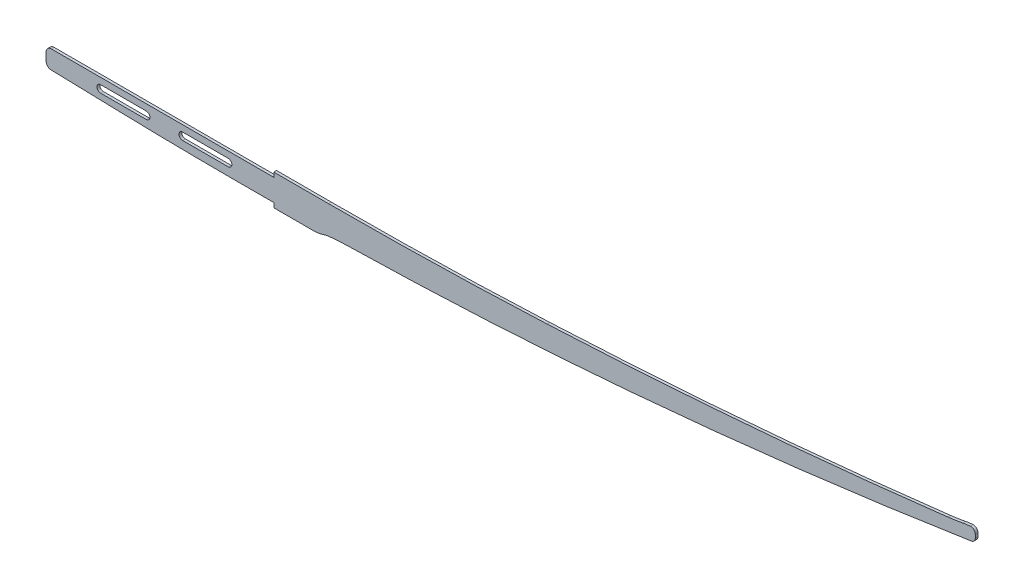
SolidWorks part; units mm, degrees
material "普通碳钢"
ref_plane "前视基准面" through (0, 0, 0) normal (0, 0, 1) x (1, 0, 0)
ref_plane "上视基准面" through (0, 0, 0) normal (0, 1, 0) x (1, 0, 0)
ref_plane "右视基准面" through (0, 0, 0) normal (1, 0, 0) x (0, 0, -1)
sketch "草图1" plane through (0, 0, 0) normal (0, 0, 1) x (1, 0, 0)
  line L0 (0, 43.7924) -> (0, -27.2669) construction
  line L1 (-61.6949, 0) -> (38.0085, 0) construction
  line L2 (0, 12) -> (-244, 12)
  line L3 (-250, 6) -> (-250, -2.1632)
  line L4 (-40, -12) -> (0, -12)
  line L5 (0, 12) -> (0, 17)
  line L7 (0, -12) -> (0, -17)
  line L9 (770, -281.4512) -> (770, 62.7188) construction
  line L10 (0, 17) -> (60, 17)
  line L11 (0, -17) -> (44.1456, -17)
  line L12 (770, 57.6754) -> (770, 54)
  line L13 (770, 62.7188) -> (770, 57.6754) construction
  line L14 (770, 57.6754) -> (770, -1560.7663) construction
  line L15 (770, 62.7188) -> (770, 57.6754) construction
  line L16 (-170, -10.2071) -> (-244.1655, -8.161)
  line L17 (-250, -8) -> (-250, -12) construction
  line L18 (-250, -12) -> (-40, -12) construction
  line L19 (-50, 1) -> (-100, 1) construction
  line L20 (-50, -3) -> (-100, -3)
  line L21 (-50, 5) -> (-100, 5)
  line L22 (-140, 1) -> (-190, 1) construction
  line L23 (-140, -3) -> (-190, -3)
  line L24 (-140, 5) -> (-190, 5)
  arc A18 (60, 17) -> (300, 22.5414) centre (60, 5217) ccw
  arc A19 (300, 22.5414) -> (740, 59.0443) centre (21.567, 6048.8282) ccw
  arc A20 (53.8173, -15.3982) -> (60, -14) centre (63.4889, -43.7964) cw
  arc A21 (60, -14) -> (80, -12.6253) centre (84.3275, -221.7638) cw
  arc A22 (80, -12.6253) -> (390, 3.83) centre (-19.3009, 4786.3474) ccw
  arc A23 (390, 3.83) -> (765.768, 49.0593) centre (-78.9907, 5483.7979) ccw
  arc A24 (770, 54) -> (765.768, 49.0593) centre (765, 54) cw
  arc A25 (770, 57.6754) -> (764.6, 62.6593) centre (765, 57.6754) ccw
  arc A26 (764.6, 62.6593) -> (756, 61.5077) centre (771.1474, -18.9204) ccw
  arc A27 (756, 61.5077) -> (740, 59.0443) centre (711.1259, 299.7762) cw
  arc A28 (740, 59.0443) -> (766.8398, 62.3246) centre (21.567, 6048.8282) ccw construction
  arc A29 (766.8398, 62.3246) -> (770, 62.7188) centre (21.567, 6048.8282) ccw construction
  arc A30 (-40, -12) -> (-170, -10.2071) centre (-40, 4701.8911) cw
  arc A31 (-244, 12) -> (-250, 6) centre (-244, 6) ccw
  arc A32 (-244.1655, -8.161) -> (-250, -2.1632) centre (-244, -2.1632) cw
  arc A33 (-50, -3) -> (-50, 5) centre (-50, 1) ccw
  arc A34 (-100, 5) -> (-100, -3) centre (-100, 1) ccw
  arc A35 (-140, -3) -> (-140, 5) centre (-140, 1) ccw
  arc A36 (-190, 5) -> (-190, -3) centre (-190, 1) ccw
  arc A37 (53.8173, -15.3982) -> (44.1456, -17) centre (44.1456, 13) cw
  point P29 (770, 49.7188)
  point P45 (-75, 1)
  point P54 (-165, 1)
  point P63 (50, -17)
  dimension "D10" = 80
  dimension "D11" = 380
  dimension "D12" = 4800
  dimension "D6" = 5200
  dimension "D8" = 5500
  dimension "D13" = 13
  dimension "D14" = 30
  dimension "D15" = 54
  dimension "D18" = 5
  dimension "D19" = 5
  dimension "D27" = 6
  dimension "D35" = 30
  dimension "D1" = 250
  dimension "D2" = 24
  dimension "D3" = 60
  dimension "D4" = 34
  dimension "D5" = 770
  dimension "D7" = 50
  dimension "D9" = 300
  dimension "D16" = 60
  dimension "D17" = 14
  dimension "D20" = 30
  dimension "D21" = 14
  dimension "D22" = 5.4
  dimension "D23" = 13.6
  dimension "D24" = 4
  dimension "D25" = 80
  dimension "D26" = 40
  dimension "D28" = 50
  dimension "D29" = 50
  dimension "D30" = 1
  dimension "D31" = 8
  dimension "D32" = 40
  dimension "D33" = 50
  dimension "D34" = 8
extrude "凸台-拉伸1" add sketch "草图1" along normal mid plane 3
